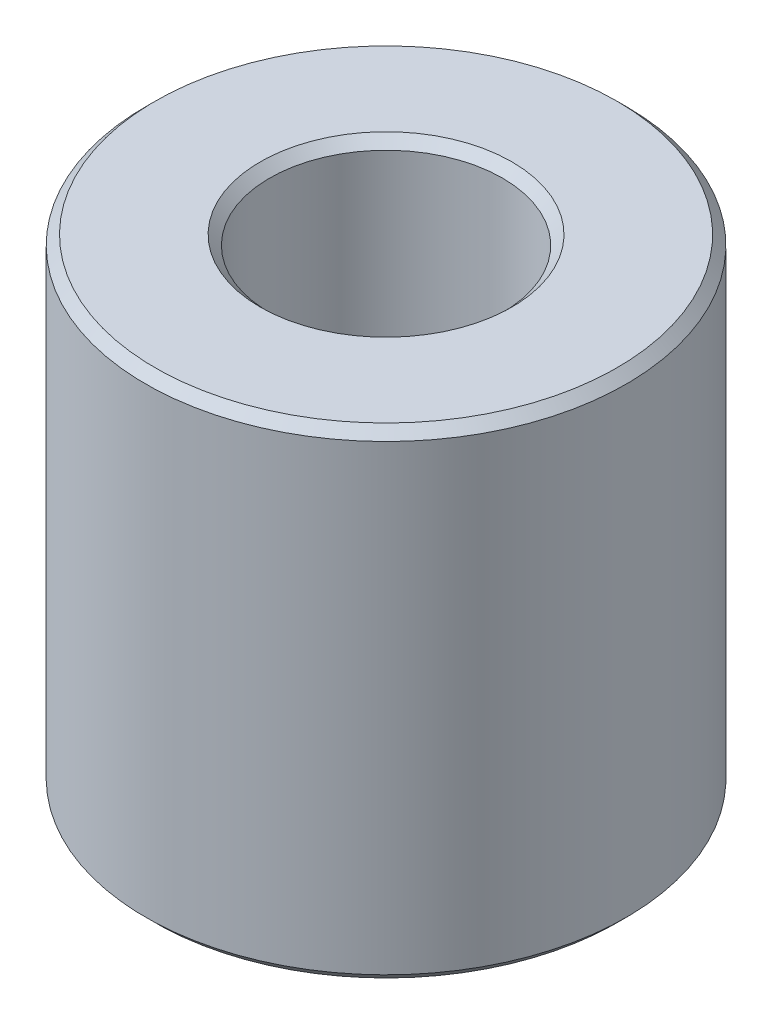
SolidWorks part; units mm, degrees
material "6061-T6 (SS)"
ref_plane "Front Plane" through (0, 0, 0) normal (0, 0, 1) x (1, 0, 0)
ref_plane "Top Plane" through (0, 0, 0) normal (0, 1, 0) x (1, 0, 0)
ref_plane "Right Plane" through (0, 0, 0) normal (1, 0, 0) x (0, 0, -1)
sketch "Sketch1" plane through (0, 0, 0) normal (0, 0, 1) x (1, 0, 0)
  line L0 (0, 0) -> (0, 33.4937) construction
  line L1 (6.246, 13) -> (6.5, 12.746)
  line L2 (3.404, 0) -> (6.246, 0)
  line L3 (3.15, 0.254) -> (3.15, 12.746)
  line L4 (3.404, 13) -> (6.246, 13)
  line L5 (6.5, 0.254) -> (6.5, 12.746)
  line L6 (6.246, 0) -> (6.5, 0.254)
  line L7 (3.15, 0.254) -> (3.404, 0)
  line L8 (3.15, 12.746) -> (3.404, 13)
  point P3 (3.15, 0)
  point P4 (6.5, 13)
  point P5 (3.15, 13)
  point P6 (6.5, 0)
  dimension "D1" = 6.3
  dimension "D2" = 13
  dimension "D3" = 13
revolve "Revolve1" add sketch "Sketch1" angle 360 about L0
